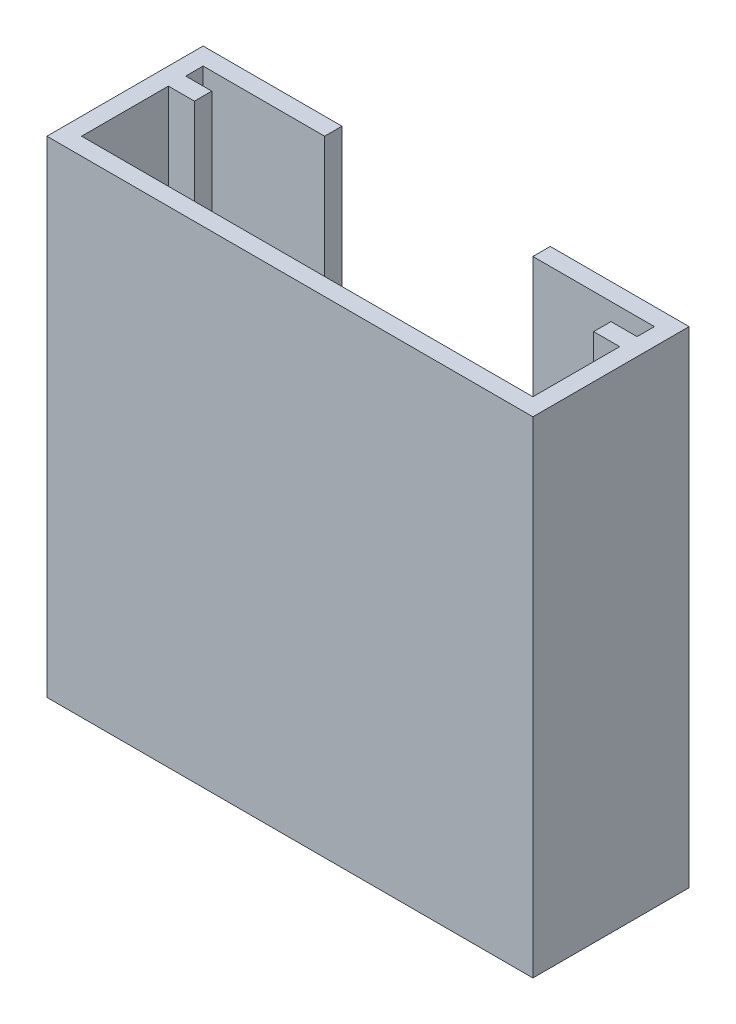
SolidWorks part; units mm, degrees
ref_plane "정면" through (0, 0, 0) normal (0, 0, 1) x (1, 0, 0)
ref_plane "윗면" through (0, 0, 0) normal (0, 1, 0) x (1, 0, 0)
ref_plane "우측면" through (0, 0, 0) normal (1, 0, 0) x (0, 0, -1)
sketch "스케치1" plane through (0, 0, 0) normal (0, 0, 1) x (1, 0, 0)
  line L0 (20, 0) -> (28, 0)
  line L2 (0, 0) -> (0, -28)
  line L3 (0, -28) -> (28, -28)
  line L4 (28, 0) -> (28, -28)
  line L6 (8, 0) -> (8, -23)
  line L7 (8, -23) -> (20, -23)
  line L8 (20, 0) -> (20, -23)
  line L9 (8, 0) -> (0, 0)
  line L10 (14, -28) -> (14, -23) construction
  dimension "D1" = 23
  dimension "D2" = 12
  dimension "D3" = 5
  dimension "D4" = 8
  dimension "D5" = 8
extrude "보스-돌출1" add sketch "스케치1" along normal blind 1
sketch "스케치3" plane through (0, 0, 1) normal (0, 0, 1) x (1, 0, 0)
  line L1 (0, 0) -> (28, 0)
  line L2 (0, 0) -> (0, -28)
  line L3 (0, -28) -> (28, -28)
  line L4 (28, 0) -> (28, -28)
  line L5 (1, 0) -> (27, 0)
  line L6 (1, 0) -> (1, -27)
  line L7 (1, -27) -> (27, -27)
  line L8 (27, 0) -> (27, -27)
  line M9 (0, 0) -> (0, -28)
  line M10 (0, -28) -> (28, -28)
  line M11 (28, -28) -> (28, 0)
  line M12 (28, 0) -> (20, 0)
  dimension "D1" = 1
  dimension "D2" = 1
  dimension "D3" = 1
extrude "보스-돌출2" add sketch "스케치3" along normal blind 7 contours L8 L7 L6 L1 M12 M9 M10 M11
sketch "스케치5" plane through (1, 0, 0) normal (1, 0, 0) x (0, 0, -1)
  line L0 (-8, 0) -> (-1, 0) construction
  line L1 (-2, 0) -> (-3, 0)
  line L2 (-2, 0) -> (-2, -27)
  line L3 (-2, -27) -> (-3, -27)
  line L4 (-3, 0) -> (-3, -27)
  line L5 (-8, -27) -> (-1, -27) construction
  line L6 (-1, 0) -> (-1, -27) construction
  dimension "D1" = 1
  dimension "D2" = 1
extrude "보스-돌출3" add sketch "스케치5" along normal blind 1.5
sketch "스케치7" plane through (27, 0, 0) normal (-1, 0, 0) x (0, 0, 1)
  line L0 (8, 0) -> (1, 0) construction
  line L1 (2, 0) -> (3, 0)
  line L2 (2, 0) -> (2, -27)
  line L3 (2, -27) -> (3, -27)
  line L4 (3, 0) -> (3, -27)
  line L5 (8, -27) -> (1, -27) construction
  line L6 (1, 0) -> (1, -27) construction
  dimension "D1" = 1
  dimension "D2" = 1
extrude "보스-돌출4" add sketch "스케치7" along normal blind 1.5
sketch "스케치8" plane through (0, 0, 8) normal (0, 0, 1) x (1, 0, 0)
  line L1 (28, -28) -> (0, -28)
  line L2 (28, -28) -> (28, 0)
  line L3 (28, 0) -> (0, 0)
  line L4 (0, -28) -> (0, 0)
extrude "보스-돌출5" add sketch "스케치8" along normal blind 1
